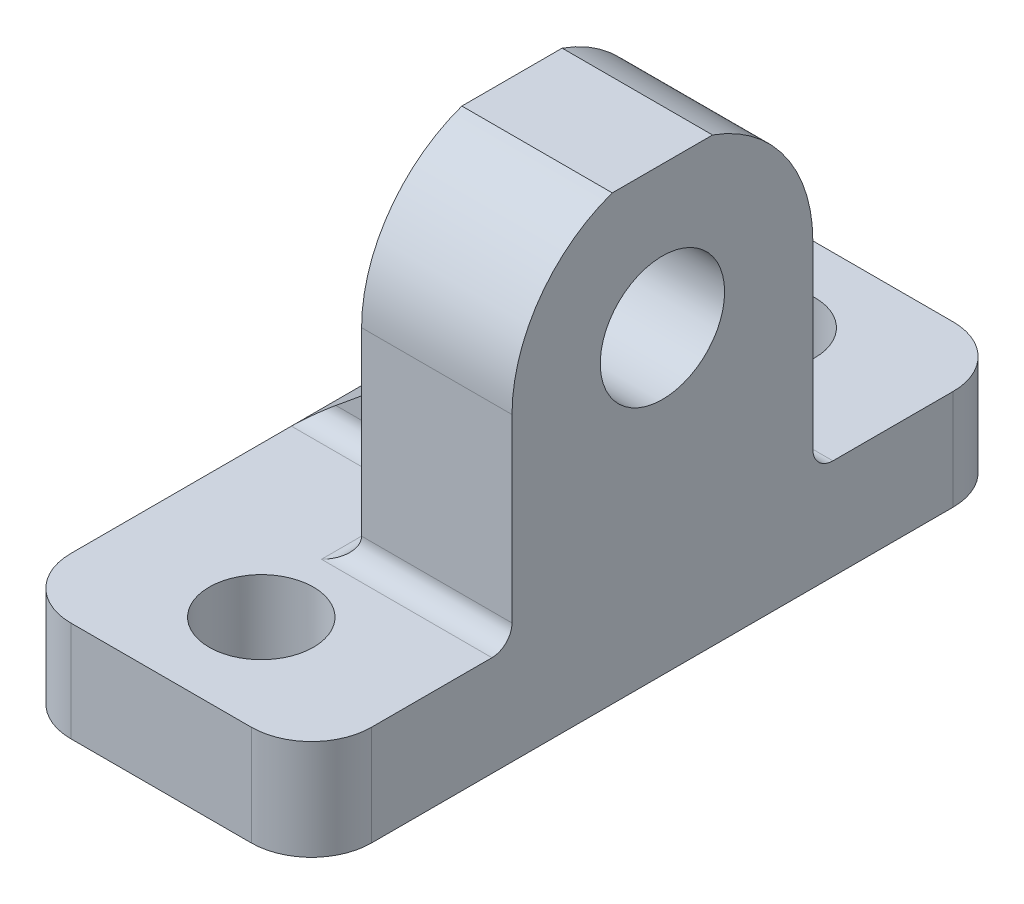
SolidWorks part; units mm, degrees
material "PBT General Purpose"
ref_plane "Front Plane" through (0, 0, 0) normal (0, 0, 1) x (1, 0, 0)
ref_plane "Top Plane" through (0, 0, 0) normal (0, 1, 0) x (1, 0, 0)
ref_plane "Right Plane" through (0, 0, 0) normal (1, 0, 0) x (0, 0, -1)
sketch "Sketch1" plane through (0, 0, 0) normal (1, 0, 0) x (0, 0, -1)
  line L0 (7.5, 2.5) -> (17.5, 2.5)
  line L1 (-17.5, -2.5) -> (17.5, -2.5)
  line L2 (-17.5, -2.5) -> (-17.5, 2.5)
  line L3 (-17.5, 2.5) -> (-7.5, 2.5)
  line L4 (17.5, -2.5) -> (17.5, 2.5)
  line L5 (-17.5, -2.5) -> (17.5, 2.5) construction
  line L6 (-17.5, 2.5) -> (17.5, -2.5) construction
  line L8 (-7.5, 12.5) -> (-7.5, 2.5)
  line L10 (7.5, 12.5) -> (7.5, 2.5)
  line L11 (-7.5, 12.5) -> (7.5, 2.5) construction
  line L12 (-7.5, 2.5) -> (7.5, 12.5) construction
  line L13 (-2.5, 19.5711) -> (2.5, 19.5711)
  arc A0 (-7.5, 12.5) -> (-2.5, 19.5711) centre (0, 12.5) cw
  circle A1 centre (0, 12.5) radius 3.1
  arc A2 (2.5, 19.5711) -> (7.5, 12.5) centre (0, 12.5) cw
  point P0 (0, 0)
  point P6 (0, 7.5)
  dimension "D6" = 6.2
  dimension "D1" = 15
  dimension "D2" = 10
  dimension "D3" = 5
  dimension "D4" = 35
  dimension "D5" = 10
  dimension "D7" = 5
extrude "Boss-Extrude1" add sketch "Sketch1" along normal blind 15
sketch "Sketch2" plane through (0, 19.5711, 0) normal (0, 1, 0) x (1, 0, 0)
  line L7 (15, 17.5) -> (0, 17.5) construction
  line L8 (15, -17.5) -> (0, -17.5) construction
  line L9 (0, 17.5) -> (0, 7.5) construction
  circle A0 centre (7.5, 12.5) radius 2.6
  circle A1 centre (7.5, -12.5) radius 2.6
  point P1 (0, 0)
  point P16 (0, 0)
  point P17 (0, 0)
  dimension "D1" = 5.2
  dimension "D2" = 5
  dimension "D3" = 5
  dimension "D4" = 7.5
extrude "Cut-Extrude2" cut sketch "Sketch2" against normal through all
sketch "Sketch3" plane through (0, 19.5711, 0) normal (0, 1, 0) x (1, 0, 0)
  line L6 (15, -2.5) -> (0, -2.5) construction
  line L7 (0, -7.5) -> (7.5, -7.5)
  line L8 (0, -7.5) -> (0, -2.5)
  line L9 (0, -2.5) -> (7.5, -2.5)
  line L10 (7.5, -7.5) -> (7.5, -2.5)
  line L11 (15, 2.5) -> (0, 2.5) construction
  line L12 (0, 7.5) -> (7.5, 7.5)
  line L13 (0, 7.5) -> (0, 2.5)
  line L14 (0, 2.5) -> (7.5, 2.5)
  line L15 (7.5, 7.5) -> (7.5, 2.5)
extrude "Cut-Extrude4" cut sketch "Sketch3" against normal up to surface (17.0711 mm away) up to face at (7.5, 2.5, 9.9)
sketch "Sketch4" plane through (0, 0, 2.5) normal (0, 0, 1) x (1, 0, 0)
  line L0 (7.5, 8.667) -> (0, 2.5)
  line L1 (0, 19.5711) -> (7.5, 19.5711)
  line L2 (0, 19.5711) -> (0, 14.333)
  line L3 (0, 14.333) -> (7.5, 14.333)
  line L4 (7.5, 19.5711) -> (7.5, 14.333)
  line L10 (0, 10.667) -> (0, 2.5)
  line L11 (0, 10.667) -> (7.5, 10.667)
  line L14 (7.5, 10.667) -> (7.5, 8.667)
  line L15 (7.5, 2.5) -> (7.5, 12.5) construction
  point P8 (0, 0)
  point P9 (9.8634, 10.1788)
  point P11 (0, 0)
  point P12 (0, 0)
  point P13 (7.5, 8.7002)
  dimension "D1" = 2
extrude "Cut-Extrude5" cut sketch "Sketch4" against normal up to surface (5 mm away) up to face at (3.75, 6.5835, -2.5)
fillet "Fillet1" radius 1 6 edges at (11.25, 2.5, 7.5) (11.25, 2.5, -7.5) (3.75, 2.5, -2.5) (7.5, 2.5, -5) (7.5, 2.5, 5) (3.75, 2.5, 2.5)
fillet "Fillet2" radius 3 4 edges at (15, 0, -17.5) (15, 0, 17.5) (0, 0, 17.5) (0, 0, -17.5)
